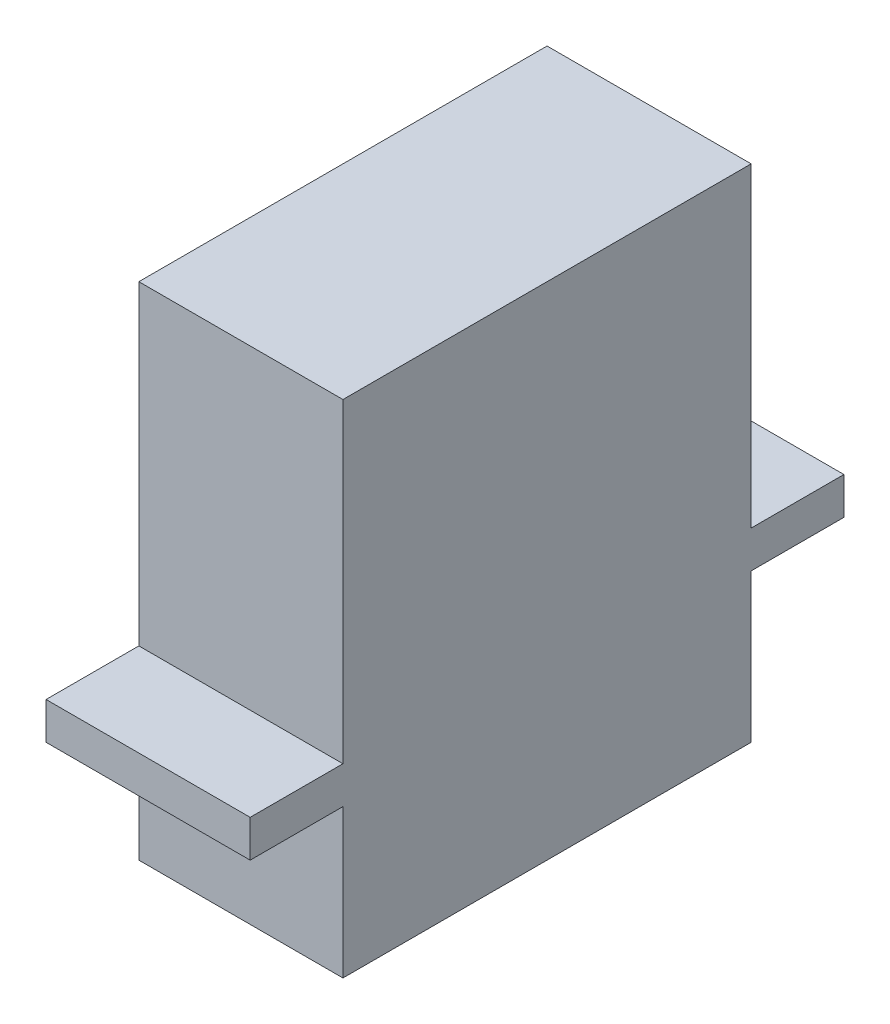
SolidWorks part; units mm, degrees
material "ABS"
ref_plane "Front Plane" through (0, 0, 0) normal (0, 0, 1) x (1, 0, 0)
ref_plane "Top Plane" through (0, 0, 0) normal (0, 1, 0) x (1, 0, 0)
ref_plane "Right Plane" through (0, 0, 0) normal (1, 0, 0) x (0, 0, -1)
sketch "Sketch1" plane through (0, 0, 0) normal (0, 1, 0) x (1, 0, 0)
  line L1 (0, 0) -> (11, 0)
  line L2 (0, 0) -> (0, 22)
  line L3 (0, 22) -> (11, 22)
  line L4 (11, 0) -> (11, 22)
  dimension "D1" = 22
  dimension "D2" = 11
extrude "Boss-Extrude1" add sketch "Sketch1" along normal blind 27
sketch "Sketch2" plane through (0, 0, 0) normal (0, -1, 0) x (1, 0, 0)
  line L0 (11, 0) -> (11, -22) construction
  line L1 (0, 0) -> (11, 0)
  line L2 (0, 0) -> (0, 5)
  line L3 (0, 5) -> (11, 5)
  line L4 (11, 0) -> (11, 5)
  line L5 (0, -22) -> (11, -22)
  line L6 (0, -22) -> (0, -27)
  line L7 (0, -27) -> (11, -27)
  line L8 (11, -22) -> (11, -27)
  point P10 (0, 0)
  dimension "D1" = 5
  dimension "D2" = 5
extrude "Boss-Extrude2" add sketch "Sketch2" against normal blind 2 from offset 8 offset against normal yes
sketch "Sketch3" plane through (0, 0, 0) normal (0, -1, 0) x (1, 0, 0)
  line L1 (11, 5) -> (0, 5) construction
  line L2 (0, 0) -> (11, 0) construction
  circle A0 centre (5.5, -5) radius 2
  point P4 (0, 0)
  point P7 (5.5, 0)
  dimension "D2" = 4
  dimension "D1" = 10
